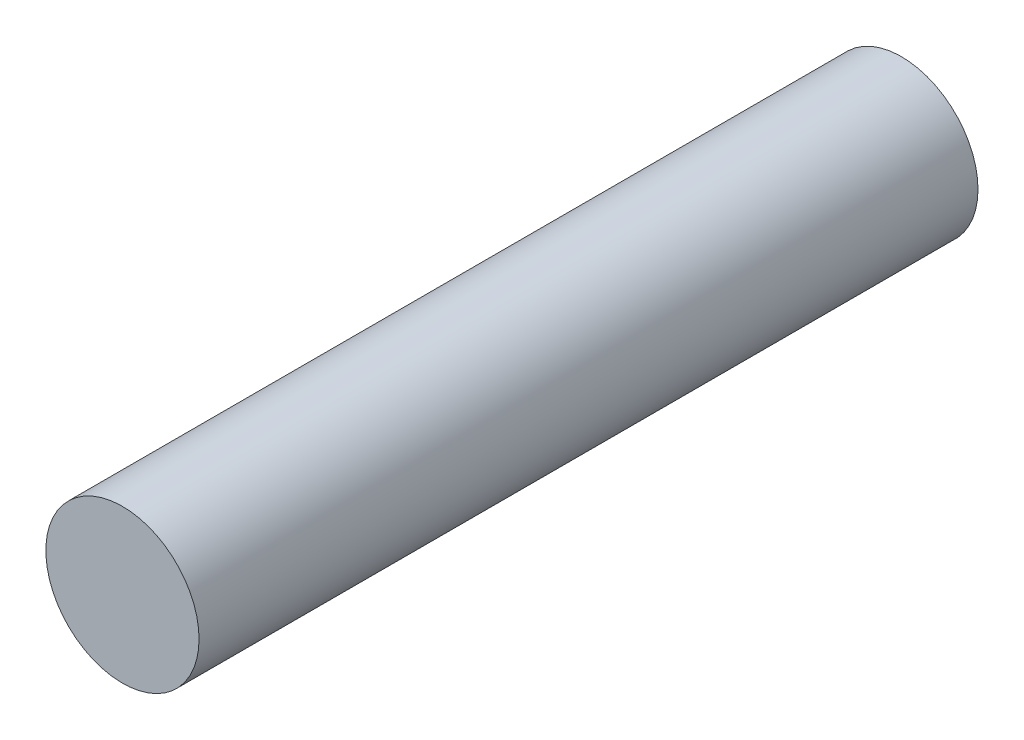
SolidWorks part; units mm, degrees
ref_plane "Front Plane" through (0, 0, 0) normal (0, 0, 1) x (1, 0, 0)
ref_plane "Top Plane" through (0, 0, 0) normal (0, 1, 0) x (1, 0, 0)
ref_plane "Right Plane" through (0, 0, 0) normal (1, 0, 0) x (0, 0, -1)
sketch "Sketch1" plane through (0, 0, 0) normal (0, 0, 1) x (1, 0, 0)
  circle A0 centre (0, 0) radius 2.95
  dimension "D1" = 5.9
extrude "Boss-Extrude1" add sketch "Sketch1" along normal blind 30
sketch "Sketch2" plane through (0, 0, 0) normal (0, 0, -1) x (-1, 0, 0)
  line L0 (-1.3497, 1.435) -> (1.3497, 1.435)
  arc A0 (-1.3497, 1.435) -> (1.3497, 1.435) centre (0, 0) ccw
  dimension "D1" = 1.435
  dimension "D2" = 1.97
extrude "Cut-Extrude1" cut sketch "Sketch2" against normal blind 7
